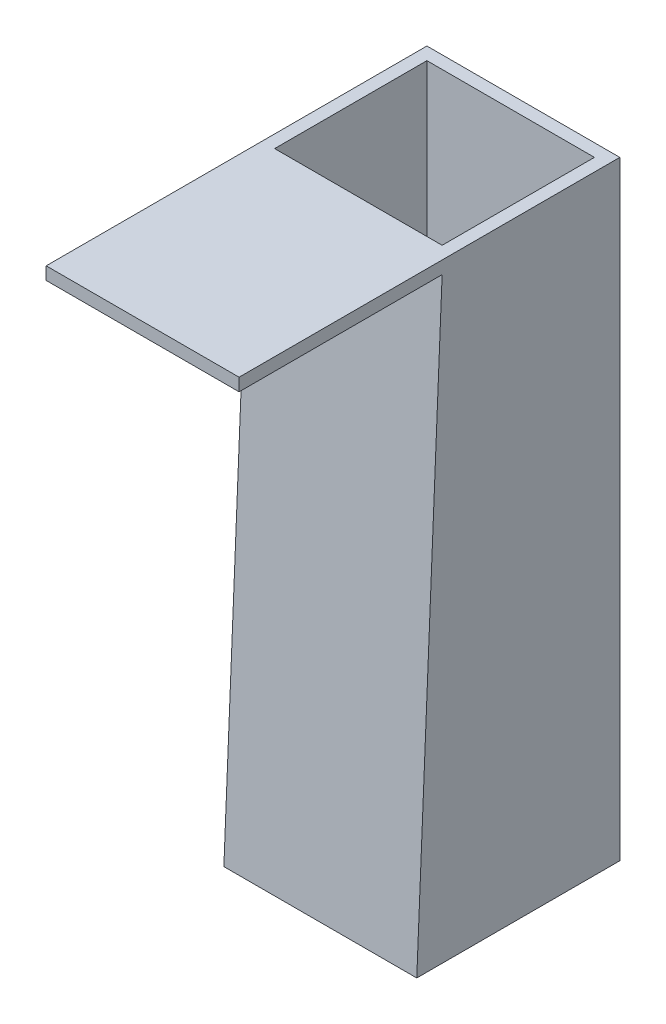
SolidWorks part; units mm, degrees
ref_plane "Front Plane" through (0, 0, 0) normal (0, 0, 1) x (1, 0, 0)
ref_plane "Top Plane" through (0, 0, 0) normal (0, 1, 0) x (1, 0, 0)
ref_plane "Right Plane" through (0, 0, 0) normal (1, 0, 0) x (0, 0, -1)
sketch "Sketch1" plane through (0, 0, 0) normal (1, 0, 0) x (0, 0, -1)
  line L0 (0, 0) -> (12.7, 298.45)
  line L1 (12.7, 298.45) -> (-88.9, 298.45)
  line L2 (-88.9, 298.45) -> (-88.9, 304.8)
  line L3 (-88.9, 304.8) -> (101.6, 304.8)
  line L4 (101.6, 304.8) -> (101.6, 0)
  line L5 (101.6, 0) -> (0, 0)
  dimension "D1" = 304.8
  dimension "D2" = 88.9
  dimension "D3" = 6.35
  dimension "D4" = 101.6
  dimension "D5" = 101.6
extrude "Boss-Extrude1" add sketch "Sketch1" along normal blind 96.52 contours L1 L2 L3 L4 L5 L0
sketch "Sketch2" plane through (0, 0, 0) normal (0, -1, 0) x (1, 0, 0)
  line L0 (96.52, -101.6) -> (0, -101.6) construction
  line L1 (6.35, -95.25) -> (90.17, -95.25)
  line L2 (6.35, -95.25) -> (6.35, -19.05)
  line L3 (6.35, -19.05) -> (90.17, -19.05)
  line L4 (90.17, -95.25) -> (90.17, -19.05)
  line L5 (96.52, -101.6) -> (96.52, 0) construction
  line L6 (0, -101.6) -> (0, 0) construction
  dimension "D1" = 6.35
  dimension "D2" = 6.35
  dimension "D3" = 6.35
  dimension "D4" = 76.2
extrude "Cut-Extrude1" cut sketch "Sketch2" against normal through all
